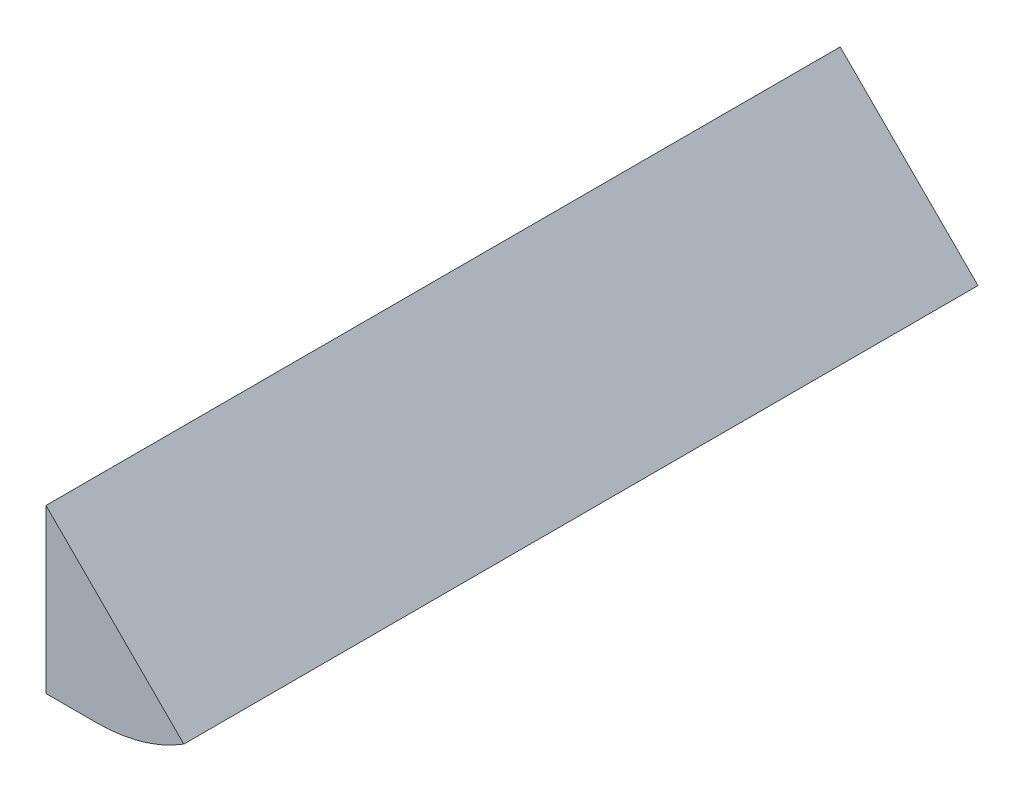
SolidWorks part; units mm, degrees
ref_plane "Спереди" through (0, 0, 0) normal (0, 0, 1) x (1, 0, 0)
ref_plane "Сверху" through (0, 0, 0) normal (0, 1, 0) x (1, 0, 0)
ref_plane "Слева" through (0, 0, 0) normal (1, 0, 0) x (0, 0, -1)
sketch "Эскиз1" plane through (0, 0, 0) normal (0, 0, 1) x (1, 0, 0)
  line L0 (-410, 16) -> (-410, 8) construction
  line L1 (-410, 16) -> (-410, 8)
  line L2 (-407.5, 8) -> (-449, 8) construction
  line L3 (-407.5, 8) -> (-449, 8) construction
  line L4 (-410, 8) -> (-402, 8) construction
  line L5 (-410, 16) -> (-403.233, 9.233)
  line L6 (-403.233, 9.233) -> (-402, 8) construction
  line L7 (-407.5, 8) -> (-410, 8)
  arc A0 (-407.5, 8) -> (-401.8431, 10.3431) centre (-407.5, 16) ccw construction
  arc A1 (-407.5, 8) -> (-403.233, 9.233) centre (-407.5, 16) ccw
  arc A2 (-403.233, 9.233) -> (-401.8431, 10.3431) centre (-407.5, 16) ccw construction
  point P5 (-403.233, 9.233)
extrude "Вытянуть1" add sketch "Эскиз1" against normal blind 39 from vertex at -11
